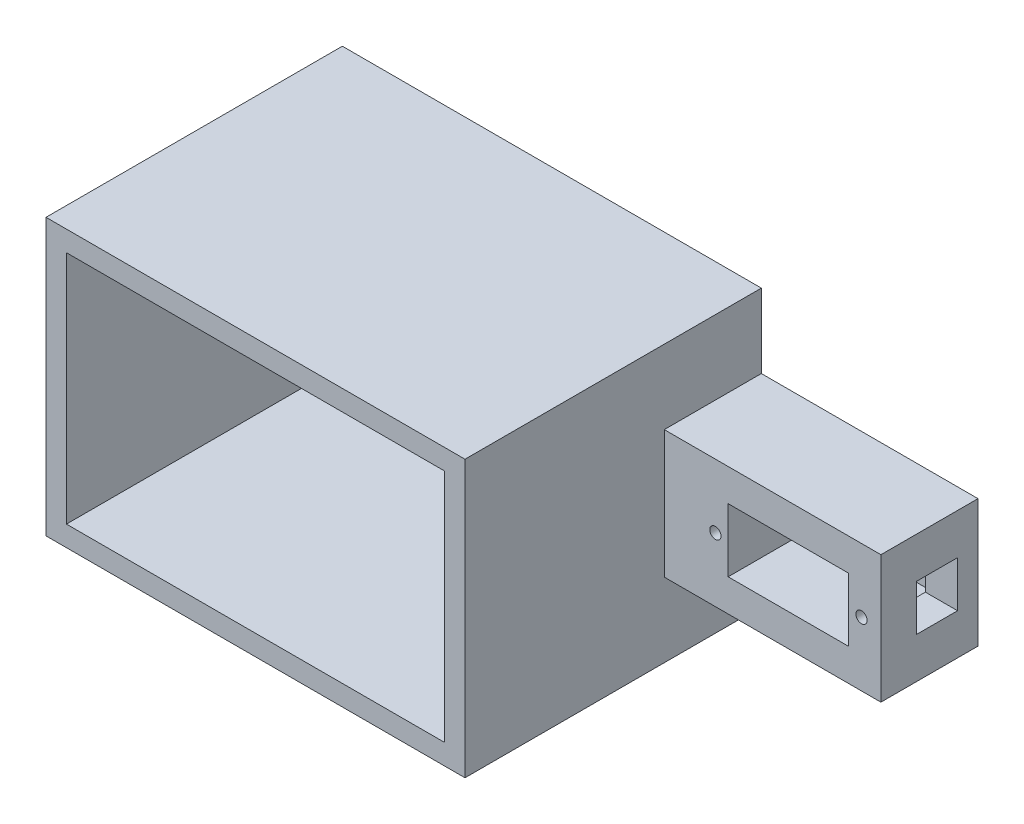
SolidWorks part; units mm, degrees
ref_plane "前基準面" through (0, 0, 0) normal (0, 0, 1) x (1, 0, 0)
ref_plane "上基準面" through (0, 0, 0) normal (0, 1, 0) x (1, 0, 0)
ref_plane "右基準面" through (0, 0, 0) normal (1, 0, 0) x (0, 0, -1)
sketch "草圖1" plane through (0, 0, 0) normal (0, 0, 1) x (1, 0, 0)
  line L5 (-65.029, 7.9036) -> (-20.029, 7.9036)
  line L6 (-65.029, 7.9036) -> (-65.029, -17.0964)
  line L7 (-65.029, -17.0964) -> (-20.029, -17.0964)
  line L8 (-20.029, 7.9036) -> (-20.029, -17.0964)
extrude "填料-伸長2" add sketch "草圖1" along normal blind 19 contours L6 L5 L8 L7
sketch "草圖4" plane through (0, 0, 19) normal (0, 0, 1) x (1, 0, 0)
  line L1 (-49.929, 1.6036) -> (-26.329, 1.6036)
  line L2 (-49.929, 1.6036) -> (-49.929, -10.7964)
  line L3 (-49.929, -10.7964) -> (-26.329, -10.7964)
  line L4 (-26.329, 1.6036) -> (-26.329, -10.7964)
  line L6 (-20.029, 7.9036) -> (-20.029, -17.0964) construction
  dimension "D1" = 6.3
extrude "除料-伸長2" cut sketch "草圖4" against normal blind 17.5
sketch "草圖5" plane through (-20.029, 0, 0) normal (1, 0, 0) x (0, 0, -1)
  line L0 (-19, 7.9036) -> (0, 7.9036) construction
  line L1 (-12, -0.0964) -> (-4, -0.0964)
  line L2 (-12, -0.0964) -> (-12, -9.0964)
  line L3 (-12, -9.0964) -> (-4, -9.0964)
  line L4 (-4, -0.0964) -> (-4, -9.0964)
  line L5 (0, 7.9036) -> (0, -17.0964) construction
  line L6 (-19, -17.0964) -> (0, -17.0964) construction
  dimension "D1" = 8
  dimension "D2" = 8
  dimension "D3" = 4
extrude "除料-伸長4" cut sketch "草圖5" against normal blind 7
sketch "草圖6" plane through (0, 0, 19) normal (0, 0, 1) x (1, 0, 0)
  line L0 (-65.029, 7.9036) -> (-20.029, 7.9036) construction
  line L1 (-26.329, -10.7964) -> (-26.329, 1.6036) construction
  line L2 (-49.929, 1.6036) -> (-49.929, -10.7964) construction
  circle A0 centre (-23.829, -4.5964) radius 1.1
  circle A1 centre (-52.429, -4.5964) radius 1.1
  dimension "D2" = 2.5
  dimension "D4" = 2.5
  dimension "D1" = 12.5
  dimension "D3" = 12.5
extrude "除料-伸長6" cut sketch "草圖6" against normal blind 7.5 contours A1 | A0
sketch "草圖8" plane through (0, 0, 19) normal (0, 0, 1) x (1, 0, 0)
  line L0 (-65.029, 7.9036) -> (-65.029, -17.0964) construction
  line L1 (-65.029, 7.9036) -> (-62.429, 7.9036)
  line L2 (-65.029, 7.9036) -> (-65.029, -17.0964)
  line L3 (-65.029, -17.0964) -> (-62.429, -17.0964)
  line L4 (-62.429, 7.9036) -> (-62.429, -17.0964)
  line L5 (-65.029, 7.9036) -> (-20.029, 7.9036) construction
  line L6 (-65.029, -17.0964) -> (-20.029, -17.0964) construction
extrude "填料-伸長3" add sketch "草圖8" along normal blind 17.5 contours L2 L1 L4 L3
sketch "草圖10" plane through (-62.429, 0, 0) normal (1, 0, 0) x (0, 0, -1)
  line L1 (-36.5, -34.6132) -> (-36.5, 25.3868)
  line L10 (-36.5, -34.6132) -> (0, -34.6132)
  line L11 (-36.5, -34.6132) -> (0, -34.6132)
  line L12 (-36.5, -34.6132) -> (-36.5, 25.3868)
  line L13 (-36.5, 25.3868) -> (0, 25.3868)
  line L14 (0, -34.6132) -> (0, 25.3868)
extrude "填料-伸長5" add sketch "草圖10" against normal blind 2.6 contours L12 L11 L14 L13
sketch "草圖13" plane through (-65.029, 0, 0) normal (-1, 0, 0) x (0, 0, 1)
  line L0 (36.5, 25.3868) -> (0, 25.3868) construction
  line L1 (36.5, 25.3868) -> (0, 25.3868)
  line L2 (36.5, 25.3868) -> (36.5, -34.6132)
  line L3 (36.5, -34.6132) -> (0, -34.6132)
  line L4 (0, 25.3868) -> (0, -34.6132)
  line L5 (36.5, 25.3868) -> (36.5, -34.6132) construction
extrude "填料-伸長6" add sketch "草圖13" along normal blind 1.4 contours L2 L1 L4 L3
sketch "草圖14" plane through (-62.429, 0, 0) normal (1, 0, 0) x (0, 0, -1)
  line L0 (0, -34.6132) -> (0, -17.0964) construction
  line L1 (-36.5, -34.6132) -> (0, -34.6132)
  line L2 (-36.5, -34.6132) -> (-36.5, -31.6132)
  line L3 (-36.5, -31.6132) -> (0, -31.6132)
  line L4 (0, -34.6132) -> (0, -31.6132)
extrude "除料-伸長9" cut sketch "草圖14" against normal blind 4
sketch "草圖15" plane through (-62.429, 0, 0) normal (1, 0, 0) x (0, 0, -1)
  line L0 (0, 7.9036) -> (0, 25.3868) construction
  line L1 (-36.5, 25.3868) -> (0, 25.3868)
  line L2 (-36.5, 25.3868) -> (-36.5, 22.3868)
  line L3 (-36.5, 22.3868) -> (0, 22.3868)
  line L4 (0, 25.3868) -> (0, 22.3868)
extrude "除料-伸長10" cut sketch "草圖15" against normal blind 4
sketch "草圖16" plane through (0, 0, 36.5) normal (0, 0, 1) x (1, 0, 0)
  line L0 (-66.429, 22.3868) -> (-66.429, -31.6132) construction
  line L1 (-66.429, -31.6132) -> (-62.429, -31.6132)
  line L2 (-66.429, -31.6132) -> (-66.429, 22.3868)
  line L3 (-66.429, 22.3868) -> (-62.429, 22.3868)
  line L4 (-62.429, -31.6132) -> (-62.429, 22.3868)
extrude "填料-伸長7" add sketch "草圖16" along normal blind 21.5 contours L2 L1 L4 L3
sketch "草圖17" plane through (-66.429, 0, 0) normal (-1, 0, 0) x (0, 0, 1)
  line L0 (0, -31.6132) -> (58, -31.6132) construction
  line L1 (0, 22.3868) -> (4, 22.3868)
  line L2 (0, 22.3868) -> (0, -31.6132)
  line L3 (0, -31.6132) -> (4, -31.6132)
  line L4 (4, 22.3868) -> (4, -31.6132)
extrude "填料-伸長8" add sketch "草圖17" along normal blind 78 contours L2 L1 L4 L3
sketch "草圖18" plane through (0, 0, 4) normal (0, 0, 1) x (1, 0, 0)
  line L0 (-66.429, 22.3868) -> (-66.429, -31.6132) construction
  line L1 (-144.429, 22.3868) -> (-66.429, 22.3868)
  line L2 (-144.429, 22.3868) -> (-144.429, 18.3868)
  line L3 (-144.429, 18.3868) -> (-66.429, 18.3868)
  line L4 (-66.429, 22.3868) -> (-66.429, 18.3868)
extrude "填料-伸長9" add sketch "草圖18" along normal blind 54 contours L2 L1 L4 L3
sketch "草圖19" plane through (0, 0, 4) normal (0, 0, 1) x (1, 0, 0)
  line L0 (-144.429, 18.3868) -> (-144.429, -31.6132) construction
  line L1 (-66.429, -31.6132) -> (-144.429, -31.6132)
  line L2 (-66.429, -31.6132) -> (-66.429, -27.6132)
  line L3 (-66.429, -27.6132) -> (-144.429, -27.6132)
  line L4 (-144.429, -31.6132) -> (-144.429, -27.6132)
extrude "填料-伸長10" add sketch "草圖19" along normal blind 54 contours L2 L1 L4 L3
sketch "草圖20" plane through (0, 0, 4) normal (0, 0, 1) x (1, 0, 0)
  line L0 (-66.429, -27.6132) -> (-144.429, -27.6132) construction
  line L1 (-144.429, 18.3868) -> (-140.429, 18.3868)
  line L2 (-144.429, 18.3868) -> (-144.429, -27.6132)
  line L3 (-144.429, -27.6132) -> (-140.429, -27.6132)
  line L4 (-140.429, 18.3868) -> (-140.429, -27.6132)
extrude "填料-伸長11" add sketch "草圖20" along normal blind 54 contours L2 L1 L4 L3
sketch "草圖21" plane through (-62.429, 0, 0) normal (1, 0, 0) x (0, 0, -1)
  line L0 (0, -31.6132) -> (0, -17.0964) construction
  line L1 (0, -31.6132) -> (-58, -31.6132) construction
  line L2 (-58, 22.3868) -> (0, 22.3868) construction
  line L3 (0, 7.9036) -> (0, 22.3868) construction
  circle A1 centre (-25, 12.3868) radius 3
  circle A3 centre (-25, -21.6132) radius 3
  dimension "D1" = 10
  dimension "D2" = 25
  dimension "D3" = 25
  dimension "D4" = 10
